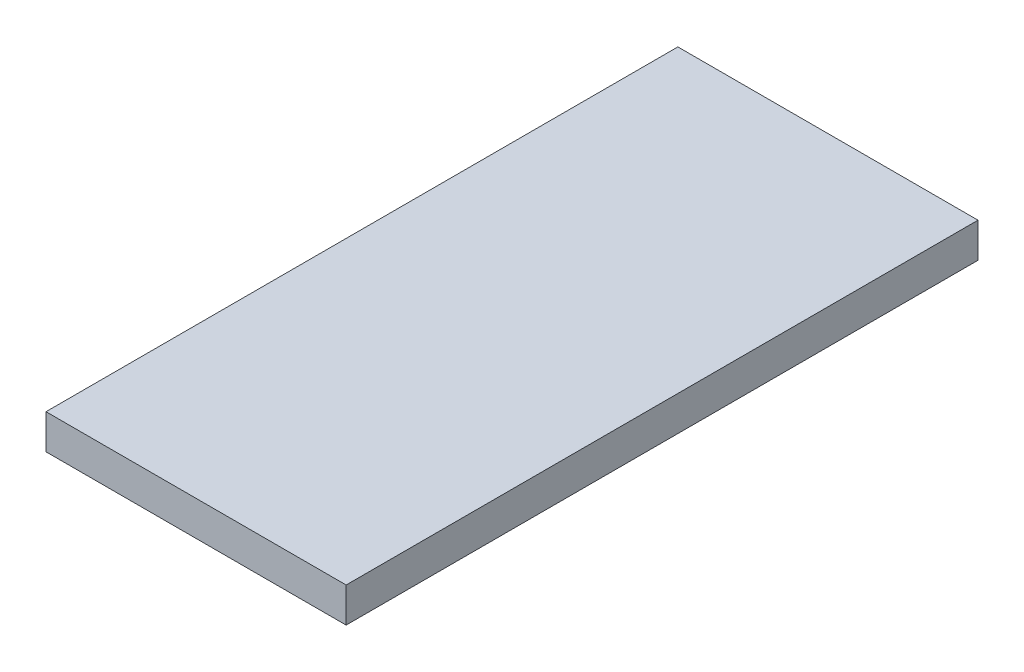
SolidWorks part; units mm, degrees
ref_plane "Front" through (0, 0, 0) normal (0, 0, 1) x (1, 0, 0)
ref_plane "Top" through (0, 0, 0) normal (0, 1, 0) x (1, 0, 0)
ref_plane "Right" through (0, 0, 0) normal (1, 0, 0) x (0, 0, -1)
sketch "Sketch1" plane through (0, 0, 0) normal (0, 0, 1) x (1, 0, 0)
  line L1 (-9.5, -1.1) -> (9.5, -1.1)
  line L2 (-9.5, -1.1) -> (-9.5, 1.1)
  line L3 (-9.5, 1.1) -> (9.5, 1.1)
  line L4 (9.5, -1.1) -> (9.5, 1.1)
  line L5 (-9.5, -1.1) -> (9.5, 1.1) construction
  line L6 (-9.5, 1.1) -> (9.5, -1.1) construction
  point P0 (0, 0)
  dimension "D1" = 19
  dimension "D2" = 2.2
extrude "Boss-Extrude1" add sketch "Sketch1" along normal blind 40
